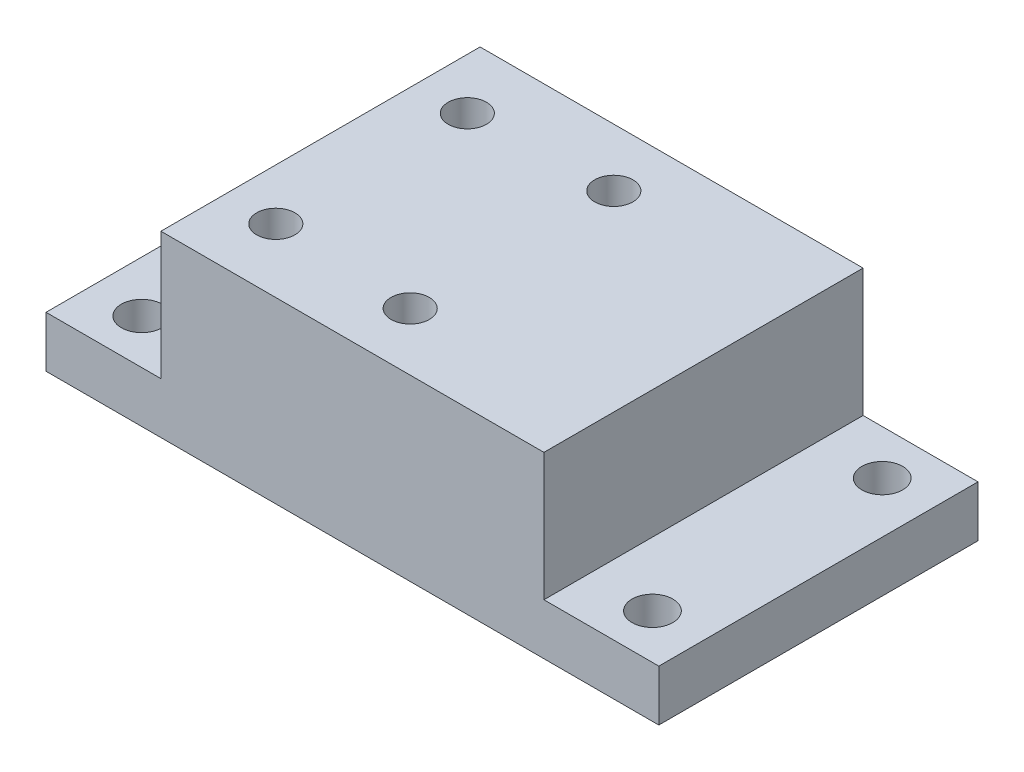
SolidWorks part; units mm, degrees
ref_plane "Спереди" through (0, 0, 0) normal (0, 0, 1) x (1, 0, 0)
ref_plane "Сверху" through (0, 0, 0) normal (0, 1, 0) x (1, 0, 0)
ref_plane "Справа" through (0, 0, 0) normal (1, 0, 0) x (0, 0, -1)
sketch "Sketch1" plane through (0, 0, 0) normal (0, 1, 0) x (1, 0, 0)
  line L1 (24, -12.5) -> (-24, -12.5)
  line L2 (24, -12.5) -> (24, 12.5)
  line L3 (24, 12.5) -> (-24, 12.5)
  line L4 (-24, -12.5) -> (-24, 12.5)
  line L5 (24, -12.5) -> (-24, 12.5) construction
  line L6 (24, 12.5) -> (-24, -12.5) construction
  point P0 (0, 0)
  dimension "D1" = 25
  dimension "D2" = 48
extrude "Boss-Extrude1" add sketch "Sketch1" along normal blind 4
sketch "Sketch2" plane through (0, 4, 0) normal (0, 1, 0) x (1, 0, 0)
  line L0 (24, 12.5) -> (-24, 12.5) construction
  line L1 (15, -12.5) -> (-15, -12.5)
  line L2 (15, -12.5) -> (15, 12.5)
  line L3 (15, 12.5) -> (-15, 12.5)
  line L4 (-15, -12.5) -> (-15, 12.5)
  line L5 (15, -12.5) -> (-15, 12.5) construction
  line L6 (15, 12.5) -> (-15, -12.5) construction
  point P0 (0, 0)
  dimension "D1" = 30
extrude "Boss-Extrude2" add sketch "Sketch2" along normal blind 10
sketch "Sketch3" plane through (0, 14, 0) normal (0, 1, 0) x (1, 0, 0)
  line L0 (0, 9.5) -> (0, 6.45) construction
  line L1 (0, -6.45) -> (0, -9.5) construction
  line L2 (0, 12.5) -> (0, -12.5) construction
  line L3 (15, 12.5) -> (-15, 12.5) construction
  line L4 (-15, -12.5) -> (15, -12.5) construction
  line L5 (15, 0) -> (-15, 0) construction
  line L6 (15, -12.5) -> (15, 12.5) construction
  line L7 (-15, 12.5) -> (-15, -12.5) construction
  line L8 (-11, 12.5) -> (-11, -12.5) construction
  circle A0 centre (0, 0) radius 9.5 construction
  circle A1 centre (0, 0) radius 6.45 construction
  circle A2 centre (0, 7.975) radius 1.5
  circle A3 centre (0, -7.975) radius 1.5
  circle A4 centre (-11, 7.5) radius 1.5
  circle A5 centre (-11, -7.5) radius 1.5
  dimension "D1" = 19
  dimension "D2" = 12.9
  dimension "D3" = 3
  dimension "D4" = 3
  dimension "D6" = 3
  dimension "D5" = 11
  dimension "D7" = 15
  dimension "D8" = 7.5
extrude "Cut-Extrude1" cut sketch "Sketch3" against normal through all
sketch "Sketch4" plane through (0, 0, 0) normal (0, -1, 0) x (1, 0, 0)
  line L1 (20, -9) -> (-20, -9) construction
  line L2 (20, -9) -> (20, 9) construction
  line L3 (20, 9) -> (-20, 9) construction
  line L4 (-20, -9) -> (-20, 9) construction
  line L5 (20, -9) -> (-20, 9) construction
  line L6 (20, 9) -> (-20, -9) construction
  circle A0 centre (-20, 9) radius 1.6
  circle A1 centre (20, 9) radius 1.6
  circle A2 centre (20, -9) radius 1.6
  circle A3 centre (-20, -9) radius 1.6
  point P0 (0, 0)
  dimension "D3" = 3.2
  dimension "D1" = 18
  dimension "D2" = 40
extrude "Cut-Extrude2" cut sketch "Sketch4" against normal through all
